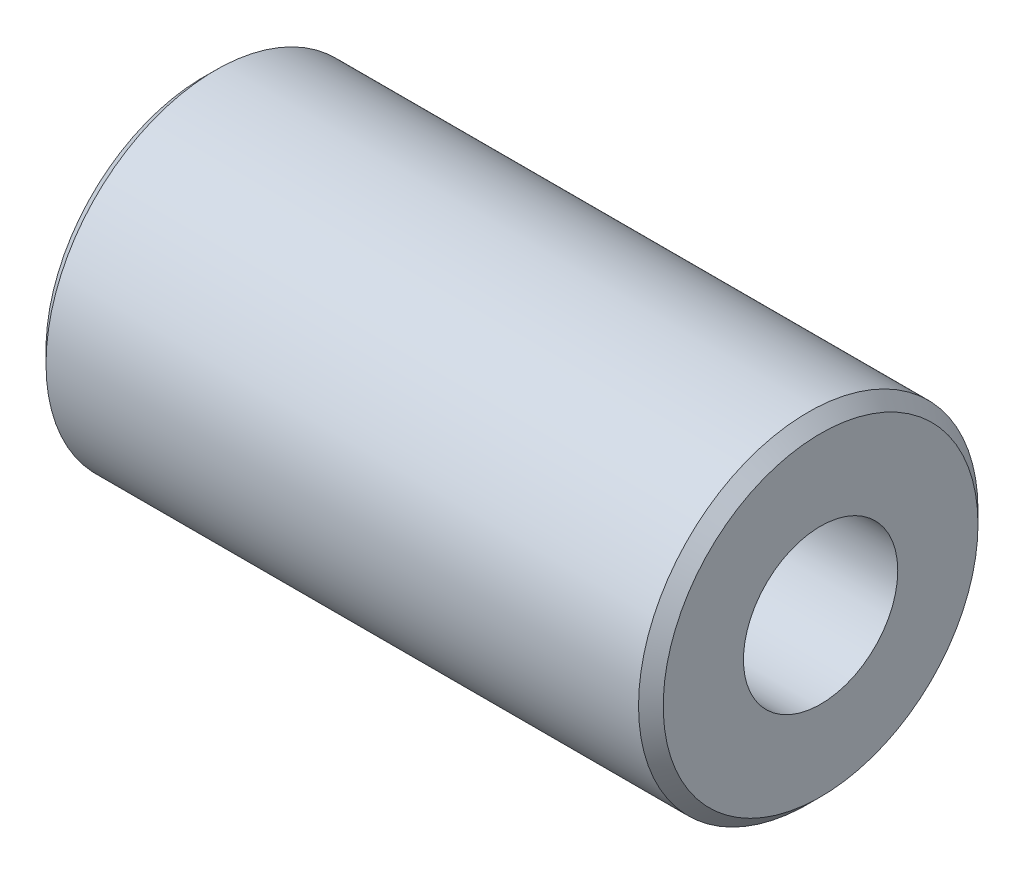
SolidWorks part; units mm, degrees
material "SUJ"
ref_plane "Front Plane" through (0, 0, 0) normal (0, 0, 1) x (1, 0, 0)
ref_plane "Top Plane" through (0, 0, 0) normal (0, 1, 0) x (1, 0, 0)
ref_plane "Right Plane" through (0, 0, 0) normal (1, 0, 0) x (0, 0, -1)
sketch "Sketch1" plane through (0, 0, 0) normal (1, 0, 0) x (0, -1, 0)
  circle A0 centre (0, 0) radius 2.75
  dimension "D1" = 5.5
extrude "Boss-Extrude1" add sketch "Sketch1" along normal mid plane 10
chamfer "Chamfer1" distance 0.2 angle 45 2 edges at (-5, 0, -2.75) (5, 0, -2.75)
hole_wizard "M3x0.5 Tapped Hole1" positions "Sketch2" profile "Sketch3" tap size "M3x0.5" standard "ANSI Metric"
sketch "Sketch2" plane through (5, 0, 0) normal (1, 0, 0) x (0, 0, -1)
  point P0 (0, 0)
sketch "Sketch3" plane through (5, 0, 0) normal (0, 1, 0) x (0, 0, -1)
  line L0 (0, 0) -> (0, 8.2511)
  line L1 (0, 8.2511) -> (1.25, 7.5)
  line L2 (1.25, 7.5) -> (1.25, 0)
  line L5 (1.25, 0) -> (0, 0)
  line L10 (0, 8.2511) -> (-1.25, 7.5) construction
  line L11 (0, -6.35) -> (0, 107.95) construction
  dimension "Tap Drill Dia." = 2.5
  dimension "Tap Drill Depth" = 7.5
  dimension "Drill Angle" = 118
cosmetic thread "Hole Thread1" parameters "D1"=6, "D2"=3
